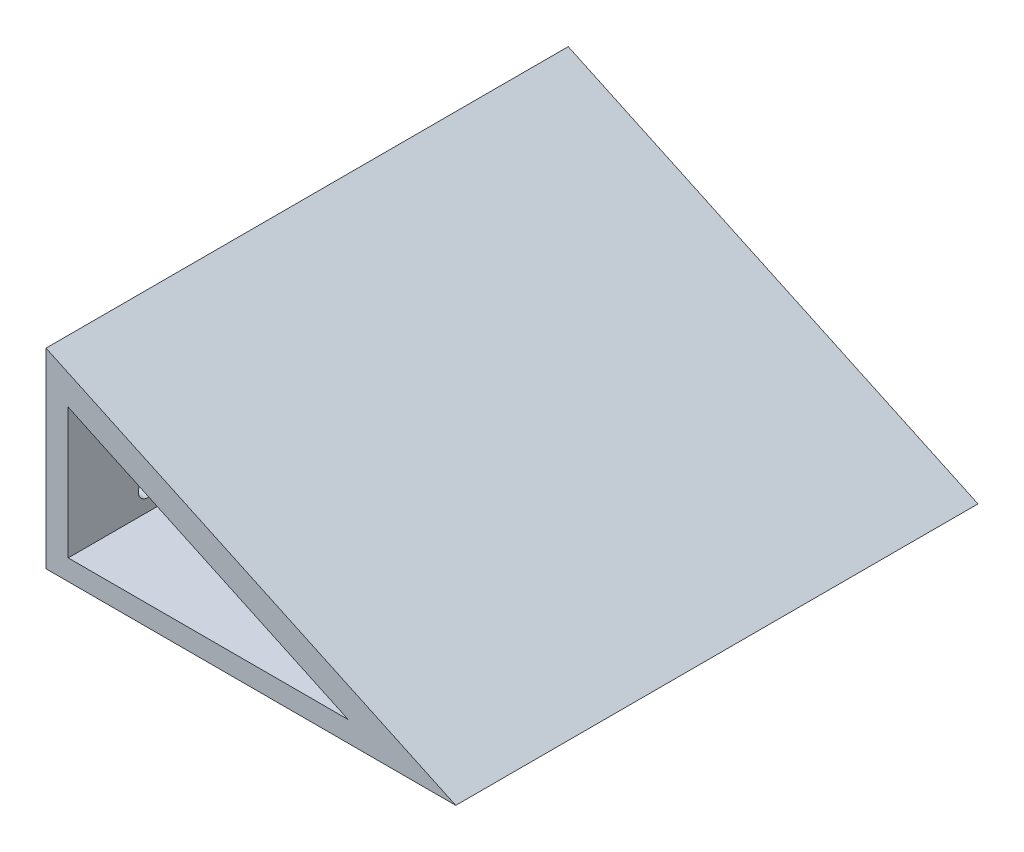
SolidWorks part; units mm, degrees
ref_plane "Front Plane" through (0, 0, 0) normal (0, 0, 1) x (1, 0, 0)
ref_plane "Top Plane" through (0, 0, 0) normal (0, 1, 0) x (1, 0, 0)
ref_plane "Right Plane" through (0, 0, 0) normal (1, 0, 0) x (0, 0, -1)
sketch "Sketch2" plane through (0, 0, 0) normal (0, 1, 0) x (1, 0, 0)
  line L1 (-128.65, 163.95) -> (128.65, 163.95)
  line L2 (-128.65, 163.95) -> (-128.65, -163.95)
  line L3 (-128.65, -163.95) -> (128.65, -163.95)
  line L4 (128.65, 163.95) -> (128.65, -163.95)
  line L5 (-128.65, 163.95) -> (128.65, -163.95) construction
  line L6 (-128.65, -163.95) -> (128.65, 163.95) construction
  point P0 (0, 0)
  dimension "D1" = 327.9
  dimension "D2" = 257.3
extrude "Boss-Extrude1" add sketch "Sketch2" along normal blind 120 contours L2 L1 L4 L3
sketch "Sketch3" plane through (0, 0, 163.95) normal (0, 0, 1) x (1, 0, 0)
  line L0 (128.65, 0) -> (-128.65, 120)
  line L1 (-128.65, 120) -> (128.65, 120)
  line L2 (128.65, 120) -> (128.65, 0)
extrude "Cut-Extrude1" cut sketch "Sketch3" against normal blind 330
sketch "Sketch4" plane through (0, 0, 163.95) normal (0, 0, 1) x (1, 0, 0)
  line L0 (-114.7031, 94.8945) -> (-114.7031, 12.8945)
  line L1 (-114.7031, 12.8945) -> (61.0969, 12.8945)
  line L2 (61.0969, 12.8945) -> (-114.7031, 94.8945)
extrude "Cut-Extrude2" cut sketch "Sketch4" against normal blind 425
sketch "Sketch5" plane through (-128.65, 0, 0) normal (-1, 0, 0) x (0, 0, 1)
  line L0 (-163.95, 120) -> (-163.95, 0) construction
  line L1 (163.95, 120) -> (163.95, 0) construction
  circle A0 centre (-114.05, 80) radius 6
  circle A1 centre (-114.05, 26.7) radius 6
  circle A2 centre (113.95, 80) radius 6
  circle A3 centre (113.95, 26.7) radius 6
  dimension "D1" = 49.9
  dimension "D2" = 50
extrude "Cut-Extrude3" cut sketch "Sketch5" against normal blind 21
